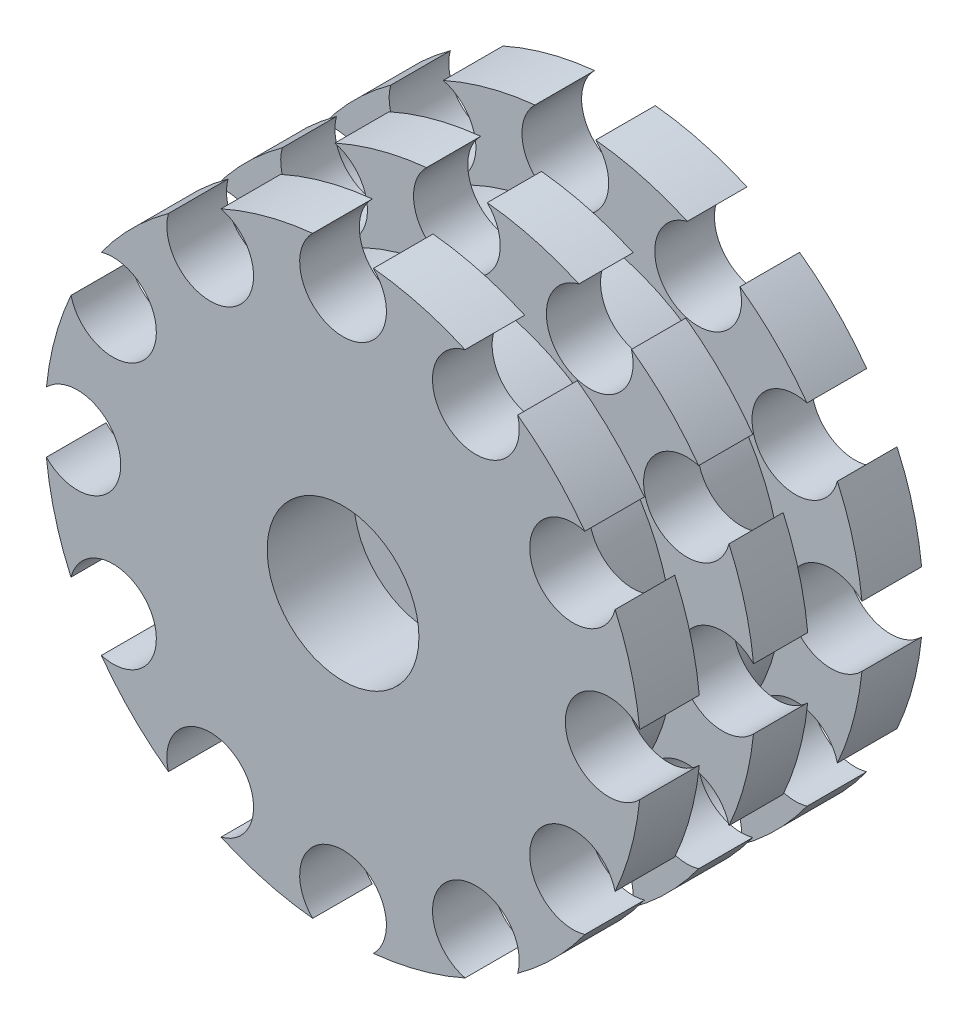
SolidWorks part; units mm, degrees
material "ABS"
ref_plane "Alzado" through (0, 0, 0) normal (0, 0, 1) x (1, 0, 0)
ref_plane "Planta" through (0, 0, 0) normal (0, 1, 0) x (1, 0, 0)
ref_plane "Vista lateral" through (0, 0, 0) normal (1, 0, 0) x (0, 0, -1)
sketch "Croquis1" plane through (0, 0, 0) normal (0, 1, 0) x (1, 0, 0)
  line L0 (0, 0) -> (0, 50000) construction
  line L1 (0, 1.5) -> (0, -9.5)
  line L3 (7, -9.5) -> (7, -13)
  line L4 (0, -9.5) -> (7, -9.5)
  line L5 (12.5, 13) -> (27.5, 13)
  line L6 (27.5, 13) -> (27.5, 7.5)
  line L7 (27.5, -2.5) -> (27.5, 2.5)
  line L8 (27.5, 2.5) -> (20, 2.5)
  line L9 (20, 2.5) -> (20, 7.5)
  line L10 (20, 7.5) -> (27.5, 7.5)
  line L12 (20, -7.5) -> (27.5, -7.5)
  line L13 (20, -2.5) -> (20, -7.5)
  line L14 (27.5, -2.5) -> (20, -2.5)
  line L15 (27.5, -13) -> (27.5, -7.5)
  line L16 (12.5, -13) -> (27.5, -13)
  line L27 (0, 1.5) -> (7.5, 1.5)
  line L28 (7.5, 1.5) -> (0, 1.5) construction
  line L29 (12.5, 6.5) -> (12.5, 13)
  line L32 (7, -13) -> (12.5, -13)
  line L37 (12.5, 6.5) -> (7.5, 1.5)
  line L38 (12.5, 6.5) -> (12.5, 13) construction
  point P22 (27.5, 0)
revolve "Revolución1" add sketch "Croquis1" angle 360 about L0
sketch "Croquis2" plane through (0, 0, -1.5) normal (0, 0, -1) x (-1, 0, 0)
  line L1 (7.5056, 0) -> (3.7528, 6.5)
  line L2 (3.7528, 6.5) -> (-3.7528, 6.5)
  line L3 (-3.7528, 6.5) -> (-7.5056, 0)
  line L4 (-7.5056, 0) -> (-3.7528, -6.5)
  line L5 (-3.7528, -6.5) -> (3.7528, -6.5)
  line L6 (3.7528, -6.5) -> (7.5056, 0)
  circle A0 centre (0, 0) radius 6.5 construction
extrude "Cortar-Extruir1" cut sketch "Croquis2" against normal blind 9
sketch "Croquis5" plane through (0, 0, 13) normal (0, 0, 1) x (1, 0, 0)
  line L0 (0, 0) -> (0, 27.5) construction
  line L1 (0, 27.5) -> (0, 24.5) construction
  circle A0 centre (0, 0) radius 27.5 construction
  circle A1 centre (0, 24.5) radius 4
  circle A2 centre (12.25, 21.2176) radius 4
  circle A3 centre (21.2176, 12.25) radius 4
  circle A4 centre (24.5, 0) radius 4
  circle A5 centre (21.2176, -12.25) radius 4
  circle A6 centre (12.25, -21.2176) radius 4
  circle A7 centre (0, -24.5) radius 4
  circle A8 centre (-12.25, -21.2176) radius 4
  circle A9 centre (-21.2176, -12.25) radius 4
  circle A10 centre (-24.5, 0) radius 4
  circle A11 centre (-21.2176, 12.25) radius 4
  circle A12 centre (-12.25, 21.2176) radius 4
  point P33 (0, 0)
  dimension "D1" = 12
extrude "Cortar-Extruir3" cut sketch "Croquis5" against normal through all
sketch "Croquis6" plane through (0, 0, 7.5) normal (0, 0, -1) x (-1, 0, 0)
  circle A0 centre (0, 0) radius 2
extrude "Cortar-Extruir4" cut sketch "Croquis6" against normal blind 10
sketch "Croquis7" plane through (0, 0, 7.5) normal (0, 0, -1) x (-1, 0, 0)
  line L6 (3.7528, -6.5) -> (7.5056, 0)
  line L7 (7.5056, 0) -> (3.7528, 6.5)
  line L8 (3.7528, 6.5) -> (-3.7528, 6.5)
  line L9 (-3.7528, 6.5) -> (-7.5056, 0)
  line L10 (-7.5056, 0) -> (-3.7528, -6.5)
  line L11 (-3.7528, -6.5) -> (3.7528, -6.5)
  line L12 (3.7528, -6.5) -> (7.5056, 0)
  line L13 (7.5056, 0) -> (3.7528, 6.5)
  line L14 (3.7528, 6.5) -> (-3.7528, 6.5)
  line L15 (-3.7528, 6.5) -> (-7.5056, 0)
  line L16 (-7.5056, 0) -> (-3.7528, -6.5)
  line L17 (-3.7528, -6.5) -> (3.7528, -6.5)
  circle A0 centre (0, 0) radius 2
  dimension "D1" = 0
extrude "Saliente-Extruir1" add sketch "Croquis7" along normal blind 4.5
sketch "Croquis8" plane through (0, 0, 9.5) normal (0, 0, 1) x (1, 0, 0)
  circle A0 centre (0, 0) radius 2
  circle A1 centre (0, 0) radius 7
extrude "Cortar-Extruir5" cut sketch "Croquis8" against normal blind 4.5
